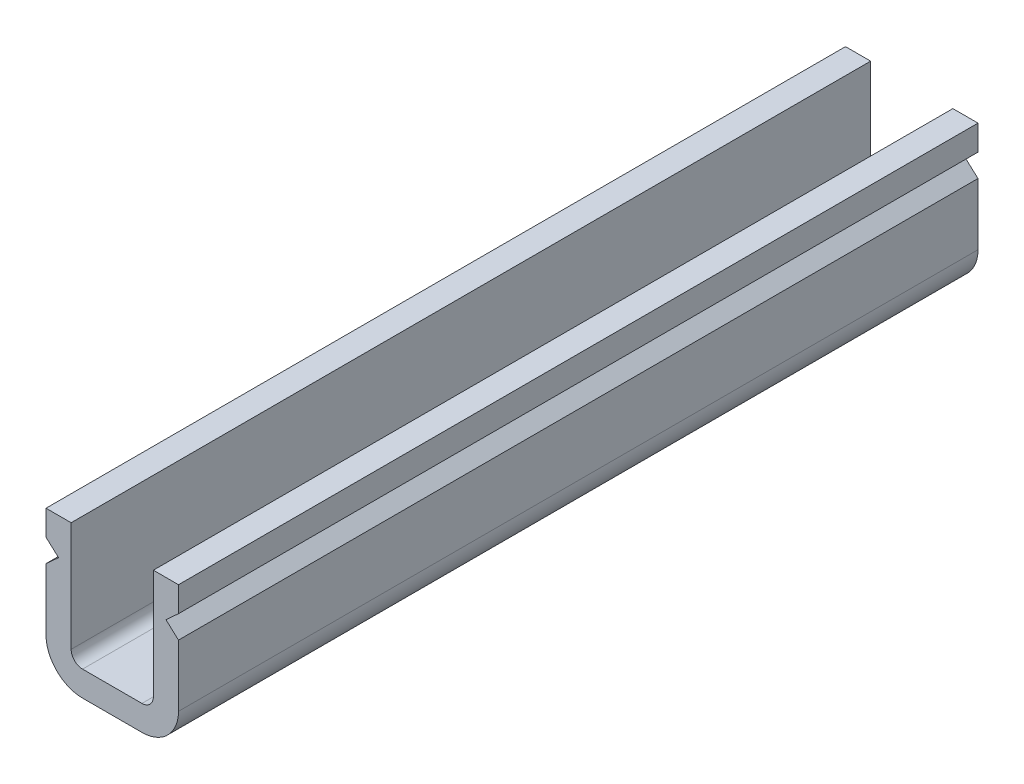
SolidWorks part; units mm, degrees
ref_plane "Plan de face" through (0, 0, 0) normal (0, 0, 1) x (1, 0, 0)
ref_plane "Plan de dessus" through (0, 0, 0) normal (0, 1, 0) x (1, 0, 0)
ref_plane "Plan de droite" through (0, 0, 0) normal (1, 0, 0) x (0, 0, -1)
sketch "Esquisse1" plane through (0, 0, 0) normal (0, 0, 1) x (1, 0, 0)
  line L4 (6.8, -6.9) -> (6.8, -2.1)
  line L22 (7.9, -3.2) -> (7.9, -2.1)
  line L23 (7.9, -4.2) -> (7.35, -3.7)
  line L24 (2.1, -2.1) -> (2.1, -3.2)
  line L25 (3.7, -8.5) -> (6.3, -8.5)
  line L26 (7.9, -6.9) -> (7.9, -4.2)
  line L27 (7.9, -2.1) -> (6.8, -2.1)
  line L28 (7.9, -3.2) -> (7.35, -3.7)
  line L29 (6.8, -7.4) -> (6.8, -4.6866) construction
  line L30 (3.2, -3.2) -> (3.2, -7.4) construction
  line L31 (3.2, -2.1) -> (2.1, -2.1)
  line L32 (7.9, -2.1) -> (2.1, -2.1) construction
  line L33 (3.2, -2.1) -> (3.2, -6.9)
  line L34 (3.7, -7.4) -> (6.3, -7.4)
  line L35 (6.8, -4.6866) -> (5.7147, -3.7) construction
  line L36 (6.2647, -3.2) -> (5.7147, -3.7) construction
  line L37 (6.2647, -3.2) -> (3.2, -3.2) construction
  line L38 (6.2647, -3.2) -> (6.2647, -3.2) construction
  line L39 (3.2, -7.4) -> (6.8, -7.4) construction
  line L40 (2.1, -3.2) -> (2.65, -3.7)
  line L41 (2.1, -4.2) -> (2.65, -3.7)
  line L42 (2.1, -4.2) -> (2.1, -6.9)
  line L43 (2.1, -2.1) -> (2.1, -8.5) construction
  line L44 (2.1, -8.5) -> (7.9, -8.5) construction
  line L45 (7.9, -8.5) -> (7.9, -4.2) construction
  arc A0 (3.2, -6.9) -> (3.7, -7.4) centre (3.7, -6.9) ccw
  arc A5 (6.8, -6.9) -> (6.3, -7.4) centre (6.3, -6.9) cw
  arc A6 (2.1, -6.9) -> (3.7, -8.5) centre (3.7, -6.9) ccw
  arc A7 (6.3, -8.5) -> (7.9, -6.9) centre (6.3, -6.9) ccw
  dimension "D2" = 0.5
  dimension "D4" = 1.6
extrude "Extrusion1" add sketch "Esquisse1" along normal blind 35
